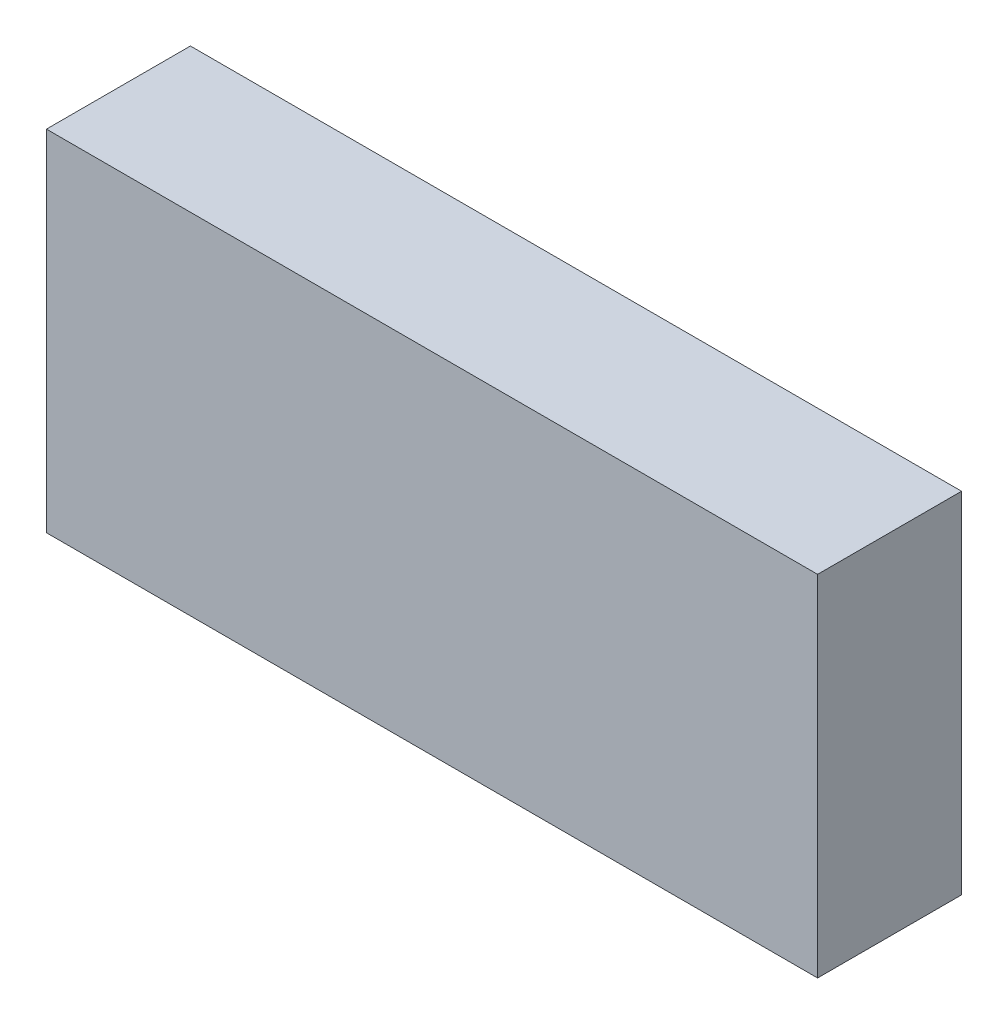
SolidWorks part; units mm, degrees
ref_plane "Front Plane" through (0, 0, 0) normal (0, 0, 1) x (1, 0, 0)
ref_plane "Top Plane" through (0, 0, 0) normal (0, 1, 0) x (1, 0, 0)
ref_plane "Right Plane" through (0, 0, 0) normal (1, 0, 0) x (0, 0, -1)
sketch "Sketch1" plane through (0, 0, 0) normal (0, 0, 1) x (1, 0, 0)
  line L1 (0, 0) -> (37.5, 0)
  line L2 (0, 0) -> (0, 17)
  line L3 (0, 17) -> (37.5, 17)
  line L4 (37.5, 0) -> (37.5, 17)
  dimension "D1" = 37.5
  dimension "D2" = 17
extrude "Boss-Extrude1" add sketch "Sketch1" along normal blind 7
